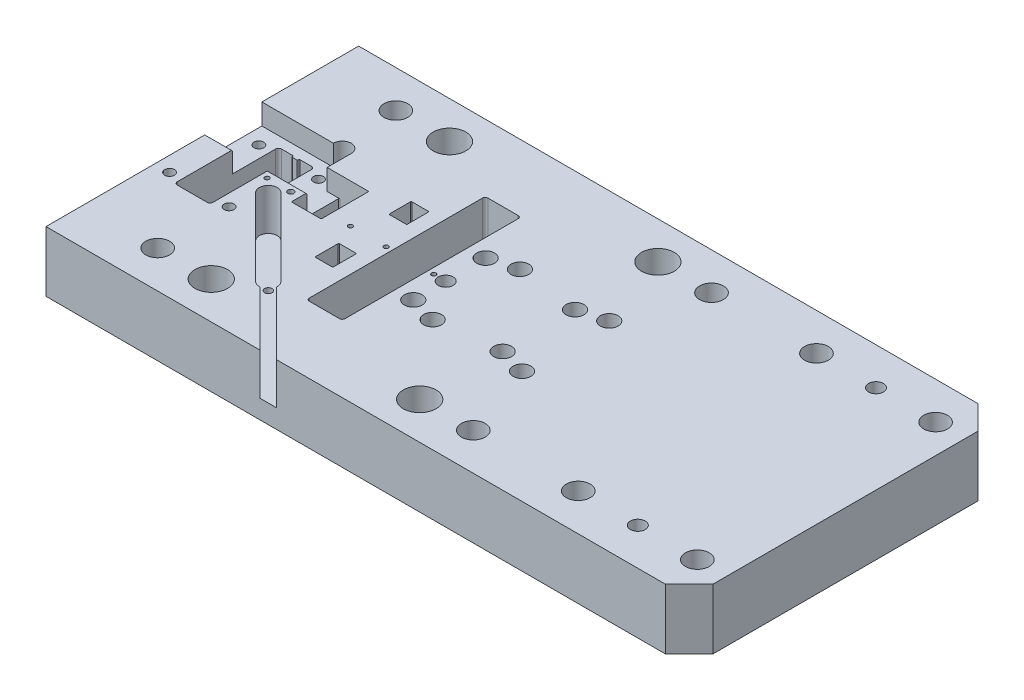
SolidWorks part; units mm, degrees
ref_plane "Front" through (0, 0, 0) normal (0, 0, 1) x (1, 0, 0)
ref_plane "Top" through (0, 0, 0) normal (0, 1, 0) x (1, 0, 0)
ref_plane "Right" through (0, 0, 0) normal (1, 0, 0) x (0, 0, -1)
sketch "Sketch1" plane through (0, 0, 0) normal (0, 0, 1) x (1, 0, 0)
  line L1 (-78, 0) -> (138, 0)
  line L2 (-78, 0) -> (-78, 20.3)
  line L3 (-78, 20.3) -> (138, 20.3)
  line L4 (138, 0) -> (138, 20.3)
  dimension "D1" = 138
  dimension "D2" = 20.3
  dimension "D3" = 78
extrude "Extrude1" add sketch "Sketch1" along normal mid plane 105
ref_plane "Plane1" through (0, 16.3, 0) normal (0, 1, 0) x (-1, 0, 0)
chamfer "Chamfer1" [suppressed] distance 0.5 angle 45
hole_wizard "M6 Tapped Hole1" [suppressed] positions "Sketch9" profile "Sketch8" tap size "M6" standard "ISO"
sketch "Sketch9" plane through (9.0333, 18, 0.7036) normal (0, -1, 0) x (1, 0, 0)
  line L4 (-9.0333, -0.7036) -> (-9.0333, -58.1038) construction
  point P0 (-44.0333, -38.2036)
  dimension "D2" = 37.5
  dimension "D1" = 35
cosmetic thread "Cosmetic Thread1" [suppressed] parameters "D1"=18, "D2"=6
sketch "Sketch8" plane through (-35, 18, -37.5) normal (1, 0, 0) x (0, 0, 1)
  line L0 (0, 0) -> (0, 18)
  line L1 (0, 18) -> (2.5, 18)
  line L2 (2.5, 18) -> (2.5, 0)
  line L5 (2.5, 0) -> (0, 0)
  line L11 (0, -6.35) -> (0, 107.95) construction
  dimension "Thru Tap Drill Dia." = 5
  dimension "Thru Tap Drill Depth" = 18
pattern_linear "LPattern3" [suppressed] count 2 spacing 70 count 2 spacing 75
hole_wizard "Ø6.0 (6.000000) Diameter Hole1" [suppressed] positions "Sketch11" profile "Sketch10" hole size "Ø6.0" standard "ISO"
sketch "Sketch11" plane through (0, 18, 0) normal (0, 1, 0) x (-1, 0, 0)
  line L1 (35, -37.5) -> (50, -37.5) construction
  point P0 (50, -37.5)
  dimension "D1" = 50
sketch "Sketch10" plane through (-50, 18, -37.5) normal (1, 0, 0) x (0, 0, 1)
  line L0 (0, 0) -> (0, 18)
  line L1 (0, 18) -> (3, 18)
  line L2 (3, 18) -> (3, 0)
  line L5 (3, 0) -> (0, 0)
  line L11 (0, -6.35) -> (0, 107.95) construction
  dimension "Thru Hole Dia." = 6
  dimension "Thru Hole Depth" = 18
pattern_linear "LPattern4" [suppressed] count 2 spacing 100 count 2 spacing 75
hole_wizard "CBORE for M6 Hex Socket Head Cap Screw1" positions "Sketch13" profile "Sketch12" counterbore size "M6" standard "ISO" end condition through all
sketch "Sketch13" plane through (0, 20.3, 0) normal (0, 1, 0) x (-1, 0, 0)
  line L0 (0, -52.5) -> (0, 10.8276) construction
  line L2 (-138, -52.5) -> (78, -52.5) construction
  line L3 (78, 52.5) -> (78, -52.5) construction
  point P0 (35, -40)
  dimension "D1" = 40
  dimension "D2" = 70
  dimension "D3" = 78
sketch "Sketch12" plane through (-35, 20.3, -40) normal (1, 0, 0) x (0, 0, 1)
  line L0 (0, 0) -> (0, 20.3)
  line L1 (0, 20.3) -> (3.2, 20.3)
  line L3 (3.2, 20.3) -> (3.2, 11)
  line L4 (3.2, 11) -> (5.5, 11)
  line L5 (5.5, 11) -> (5.5, 0)
  line L7 (5.5, 0) -> (0, 0)
  line L11 (0, -6.35) -> (0, 107.95) construction
  dimension "Thru Hole Dia." = 6.4
  dimension "Thru Hole Depth" = 20.3
  dimension "C'Bore Dia." = 11
  dimension "C'Bore Depth" = 11
pattern_linear "LPattern5" count 2 spacing 70 along (1, 0, 0) count 2 spacing 80 along (0, 0, 1) of "CBORE for M6 Hex Socket Head Cap Screw1"
hole_wizard "Hole1" positions "Sketch15" profile "Sketch14" legacy end condition through all
sketch "Sketch15" plane through (0, 20.3, 0) normal (0, 1, 0) x (-1, 0, 0)
  line L0 (0, -52.5) -> (0, 52.5) construction
  line L3 (0, 0) -> (37.836, 0) construction
  line L4 (78, 52.5) -> (78, -52.5) construction
  point P0 (53, -40)
  dimension "D1" = 40
  dimension "D2" = 106
  dimension "D3" = 78
sketch "Sketch14" plane through (-53, 20.3, -40) normal (1, 0, 0) x (0, 0, 1)
  line L0 (0, 0) -> (0, 20.3)
  line L1 (0, 20.3) -> (4, 20.3)
  line L2 (4, 20.3) -> (4, 0)
  line L3 (4, 0) -> (0, 0)
  line L4 (0, 110) -> (0, -10) construction
  dimension "Diameter" = 8
  dimension "Depth" = 20.3
pattern_linear "LPattern6" count 2 spacing 106 along (1, 0, 0) count 2 spacing 80 along (0, 0, 1) of "Hole1"
hole_wizard "Hole2" positions "Sketch17" profile "Sketch16" legacy end condition through all
sketch "Sketch17" plane through (0, 20.3, 0) normal (0, 1, 0) x (-1, 0, 0)
  line L0 (-35, -12.15) -> (-35, 12.15) construction
  line L1 (-35, 0) -> (0, 0) construction
  line L2 (-14, -14.65) -> (-44, -14.65) construction
  line L3 (-14, 14.65) -> (-44, 14.65) construction
  line L4 (-14, 14.65) -> (-14, -14.65) construction
  line L5 (-44, 14.65) -> (-44, -14.65) construction
  line L6 (-44, 0) -> (0, 0) construction
  line L7 (-5, -12.15) -> (-35, -12.15) construction
  point P0 (-35, 12.15)
  point P1 (-35, -12.15)
  point P9 (-5, -12.15)
  point P11 (-5, 12.15)
  point P12 (-14, -14.65)
  point P14 (-14, 14.65)
  point P16 (-44, 14.65)
  point P18 (-44, -14.65)
  dimension "D1" = 35
  dimension "D2" = 24.3
  dimension "D3" = 30
  dimension "D4" = 2.5
  dimension "D5" = 9
sketch "Sketch16" plane through (35, 20.3, 12.15) normal (1, 0, 0) x (0, 0, 1)
  line L0 (0, 0) -> (0, 20.3)
  line L1 (0, 20.3) -> (3, 20.3)
  line L2 (3, 20.3) -> (3, 0)
  line L3 (3, 0) -> (0, 0)
  line L4 (0, 110) -> (0, -10) construction
  dimension "Diameter" = 6
  dimension "Depth" = 20.3
sketch "Sketch20" plane through (0, 20.3, 0) normal (0, 1, 0) x (1, 0, 0)
  line L4 (-1.933, 30) -> (-12.067, 30)
  line L5 (-1, -29.067) -> (-1, 29.067)
  line L6 (-12.067, -30) -> (-1.933, -30)
  line L7 (-13, 29.067) -> (-13, -29.067)
  line L8 (-1.933, 30) -> (-12.067, 30)
  line L9 (-1, -29.067) -> (-1, 29.067)
  line L10 (-12.067, -30) -> (-1.933, -30)
  line L11 (-13, 29.067) -> (-13, -29.067)
  arc A4 (-1, 29.067) -> (-1.933, 30) centre (-1.933, 29.067) ccw
  arc A5 (-1.933, -30) -> (-1, -29.067) centre (-1.933, -29.067) ccw
  arc A6 (-13, -29.067) -> (-12.067, -30) centre (-12.067, -29.067) ccw
  arc A7 (-12.067, 30) -> (-13, 29.067) centre (-12.067, 29.067) ccw
  arc A8 (-1, 29.067) -> (-1.933, 30) centre (-1.933, 29.067) ccw
  arc A9 (-1.933, -30) -> (-1, -29.067) centre (-1.933, -29.067) ccw
  arc A10 (-13, -29.067) -> (-12.067, -30) centre (-12.067, -29.067) ccw
  arc A11 (-12.067, 30) -> (-13, 29.067) centre (-12.067, 29.067) ccw
  dimension "D1" = 0
extrude "Cut-Extrude2" cut sketch "Sketch20" against normal through all
hole_wizard "Hole3" positions "Sketch22" profile "Sketch21" legacy
sketch "Sketch22" plane through (0, 0, 0) normal (0, -1, 0) x (-1, 0, 0)
  point P0 (-5, -1.2694)
sketch "Sketch21" plane through (5, 0, 1.2694) normal (1, 0, 0) x (0, 0, -1)
  line L0 (0, 0) -> (0, 100)
  line L1 (0, 100) -> (2.5, 100)
  line L2 (2.5, 100) -> (2.5, 5)
  line L3 (2.5, 5) -> (4, 5)
  line L4 (4, 5) -> (4, 0)
  line L5 (4, 0) -> (0, 0)
  line L6 (0, 110) -> (0, -10) construction
  dimension "Diameter" = 5
  dimension "Depth" = 100
  dimension "C-Bore Diameter" = 8
  dimension "C-Bore Depth" = 5
sketch "Sketch23" plane through (0, 20.3, 0) normal (0, 1, 0) x (1, 0, 0)
  line L4 (-18.25, -8.1954) -> (-23.75, -8.1954)
  line L5 (-24, -8.4454) -> (-24, -15.9454)
  line L6 (-23.75, -16.1954) -> (-18.25, -16.1954)
  line L7 (-18, -15.9454) -> (-18, -8.4454)
  line L8 (-18.25, -8.1954) -> (-23.75, -8.1954)
  line L9 (-24, -8.4454) -> (-24, -15.9454)
  line L10 (-23.75, -16.1954) -> (-18.25, -16.1954)
  line L11 (-18, -15.9454) -> (-18, -8.4454)
  line L12 (-18.25, 16.15) -> (-23.75, 16.15)
  line L13 (-24, 15.9) -> (-24, 8.9)
  line L14 (-23.75, 8.65) -> (-18.25, 8.65)
  line L15 (-18, 8.9) -> (-18, 15.9)
  line L16 (-18.25, 16.15) -> (-23.75, 16.15)
  line L17 (-24, 15.9) -> (-24, 8.9)
  line L18 (-23.75, 8.65) -> (-18.25, 8.65)
  line L19 (-18, 8.9) -> (-18, 15.9)
  arc A4 (-23.75, -8.1954) -> (-24, -8.4454) centre (-23.75, -8.4454) ccw
  arc A5 (-24, -15.9454) -> (-23.75, -16.1954) centre (-23.75, -15.9454) ccw
  arc A6 (-18.25, -16.1954) -> (-18, -15.9454) centre (-18.25, -15.9454) ccw
  arc A7 (-18, -8.4454) -> (-18.25, -8.1954) centre (-18.25, -8.4454) ccw
  arc A8 (-23.75, -8.1954) -> (-24, -8.4454) centre (-23.75, -8.4454) ccw
  arc A9 (-24, -15.9454) -> (-23.75, -16.1954) centre (-23.75, -15.9454) ccw
  arc A10 (-18.25, -16.1954) -> (-18, -15.9454) centre (-18.25, -15.9454) ccw
  arc A11 (-18, -8.4454) -> (-18.25, -8.1954) centre (-18.25, -8.4454) ccw
  arc A12 (-23.75, 16.15) -> (-24, 15.9) centre (-23.75, 15.9) ccw
  arc A13 (-24, 8.9) -> (-23.75, 8.65) centre (-23.75, 8.9) ccw
  arc A14 (-18.25, 8.65) -> (-18, 8.9) centre (-18.25, 8.9) ccw
  arc A15 (-18, 15.9) -> (-18.25, 16.15) centre (-18.25, 15.9) ccw
  arc A16 (-23.75, 16.15) -> (-24, 15.9) centre (-23.75, 15.9) ccw
  arc A17 (-24, 8.9) -> (-23.75, 8.65) centre (-23.75, 8.9) ccw
  arc A18 (-18.25, 8.65) -> (-18, 8.9) centre (-18.25, 8.9) ccw
  arc A19 (-18, 15.9) -> (-18.25, 16.15) centre (-18.25, 15.9) ccw
  dimension "D1" = 0
  dimension "D2" = 0
extrude "Cut-Extrude3" cut sketch "Sketch23" against normal through all
sketch "Sketch24" plane through (0, 20.3, 0) normal (0, 1, 0) x (1, 0, 0)
  line L4 (-34.25, 11.9046) -> (-39, 11.9046)
  line L5 (-39, 11.9046) -> (-39, -4.0954)
  line L6 (-39, -4.0954) -> (-34.25, -4.0954)
  line L7 (-34, -3.8454) -> (-34, 11.6546)
  line L8 (-34.25, 11.9046) -> (-39, 11.9046)
  line L9 (-39, 11.9046) -> (-39, -4.0954)
  line L10 (-39, -4.0954) -> (-34.25, -4.0954)
  line L11 (-34, -3.8454) -> (-34, 11.6546)
  arc A2 (-34.25, -4.0954) -> (-34, -3.8454) centre (-34.25, -3.8454) ccw
  arc A3 (-34, 11.6546) -> (-34.25, 11.9046) centre (-34.25, 11.6546) ccw
  arc A4 (-34.25, -4.0954) -> (-34, -3.8454) centre (-34.25, -3.8454) ccw
  arc A5 (-34, 11.6546) -> (-34.25, 11.9046) centre (-34.25, 11.6546) ccw
  dimension "D1" = 0
extrude "Cut-Extrude4" cut sketch "Sketch24" against normal through all
sketch "Sketch25" plane through (0, 20.3, 0) normal (0, 1, 0) x (1, 0, 0)
  line L4 (-43.75, -4.0954) -> (-39, -4.0954)
  line L5 (-44, 11.6546) -> (-44, -3.8454)
  line L6 (-39, 11.9046) -> (-43.75, 11.9046)
  line L7 (-39, -4.0954) -> (-39, 11.9046)
  line L8 (-43.75, -4.0954) -> (-39, -4.0954)
  line L9 (-44, 11.6546) -> (-44, -3.8454)
  line L10 (-39, 11.9046) -> (-43.75, 11.9046)
  line L11 (-39, -4.0954) -> (-39, 11.9046)
  arc A2 (-44, -3.8454) -> (-43.75, -4.0954) centre (-43.75, -3.8454) ccw
  arc A3 (-43.75, 11.9046) -> (-44, 11.6546) centre (-43.75, 11.6546) ccw
  arc A4 (-44, -3.8454) -> (-43.75, -4.0954) centre (-43.75, -3.8454) ccw
  arc A5 (-43.75, 11.9046) -> (-44, 11.6546) centre (-43.75, 11.6546) ccw
  dimension "D1" = 0
extrude "Cut-Extrude5" cut sketch "Sketch25" against normal through all
sketch "Sketch26" plane through (0, 20.3, 0) normal (0, 1, 0) x (1, 0, 0)
  line L0 (-78, -52.5) -> (-78, 52.5) construction
  line L1 (-43.75, 1.1046) -> (-78, 1.1046)
  line L2 (-43.75, 1.1046) -> (-43.75, 11.9046)
  line L3 (-43.75, 11.9046) -> (-78, 11.9046)
  line L4 (-78, 1.1046) -> (-78, 11.9046)
  line L5 (-44, 1.3046) -> (-39, 1.3046) construction
  dimension "D1" = 0.2
extrude "Cut-Extrude6" cut sketch "Sketch26" against normal blind 7
sketch "Sketch27" plane through (0, 20.3, 0) normal (0, 1, 0) x (1, 0, 0)
  line L4 (-64.25, 16.6046) -> (-68, 16.6046)
  line L5 (-57, -17.3954) -> (-57, 15.6046)
  line L6 (-68, -18.3954) -> (-58, -18.3954)
  line L7 (-69, 15.6046) -> (-69, -17.3954)
  line L8 (-64.25, 16.6046) -> (-68, 16.6046)
  line L9 (-57, -17.3954) -> (-57, 15.6046)
  line L10 (-68, -18.3954) -> (-58, -18.3954)
  line L11 (-69, 15.6046) -> (-69, -17.3954)
  line L56 (-64, 16.2546) -> (-64, 16.3546)
  line L57 (-64, 16.2546) -> (-64, 16.3546)
  line L58 (-62.25, 16.0046) -> (-63.75, 16.0046)
  line L59 (-62.25, 16.0046) -> (-63.75, 16.0046)
  line L60 (-62, 16.3546) -> (-62, 16.2546)
  line L61 (-62, 16.3546) -> (-62, 16.2546)
  line L62 (-58, 16.6046) -> (-61.75, 16.6046)
  line L63 (-58, 16.6046) -> (-61.75, 16.6046)
  arc A4 (-57, 15.6046) -> (-58, 16.6046) centre (-58, 15.6046) ccw
  arc A5 (-58, -18.3954) -> (-57, -17.3954) centre (-58, -17.3954) ccw
  arc A6 (-69, -17.3954) -> (-68, -18.3954) centre (-68, -17.3954) ccw
  arc A7 (-68, 16.6046) -> (-69, 15.6046) centre (-68, 15.6046) ccw
  arc A8 (-57, 15.6046) -> (-58, 16.6046) centre (-58, 15.6046) ccw
  arc A9 (-58, -18.3954) -> (-57, -17.3954) centre (-58, -17.3954) ccw
  arc A10 (-69, -17.3954) -> (-68, -18.3954) centre (-68, -17.3954) ccw
  arc A11 (-68, 16.6046) -> (-69, 15.6046) centre (-68, 15.6046) ccw
  arc A56 (-64, 16.3546) -> (-64.25, 16.6046) centre (-64.25, 16.3546) ccw
  arc A57 (-64, 16.3546) -> (-64.25, 16.6046) centre (-64.25, 16.3546) ccw
  arc A58 (-64, 16.2546) -> (-63.75, 16.0046) centre (-63.75, 16.2546) ccw
  arc A59 (-64, 16.2546) -> (-63.75, 16.0046) centre (-63.75, 16.2546) ccw
  arc A60 (-62.25, 16.0046) -> (-62, 16.2546) centre (-62.25, 16.2546) ccw
  arc A61 (-62.25, 16.0046) -> (-62, 16.2546) centre (-62.25, 16.2546) ccw
  arc A62 (-61.75, 16.6046) -> (-62, 16.3546) centre (-61.75, 16.3546) ccw
  arc A63 (-61.75, 16.6046) -> (-62, 16.3546) centre (-61.75, 16.3546) ccw
  dimension "D1" = 0
extrude "Cut-Extrude7" cut sketch "Sketch27" against normal through all
chamfer "Chamfer2" distance 0.3 angle 45 2 edges at (-50.5, 20.3, -1.1046) (-73.5, 20.3, -1.1046)
hole_wizard "Hole4" positions "Sketch29" profile "Sketch28" legacy
sketch "Sketch29" plane through (0, 20.3, 0) normal (0, 1, 0) x (-1, 0, 0)
  point P0 (-1, 1.2694)
  point P3 (15, 1.2694)
  point P6 (27, 1.2694)
  point P12 (55, 1.2694)
sketch "Sketch28" plane through (1, 20.3, 1.2694) normal (1, 0, 0) x (0, 0, 1)
  line L0 (0, 0) -> (0, 3.433)
  line L1 (0, 3.433) -> (0.75, 3)
  line L2 (0.75, 3) -> (0.75, 0)
  line L4 (0.75, 0) -> (0, 0)
  line L6 (0, 3.433) -> (-0.75, 3) construction
  line L7 (0, -4.2442) -> (0, 117.3081) construction
  dimension "Diameter" = 1.5
  dimension "Depth" = 3
  dimension "Drill Angle" = 120
sketch "Sketch30" plane through (0, 20.3, 0) normal (0, 1, 0) x (1, 0, 0)
  line L1 (-78, 11.9046) -> (-48, 11.9046)
  line L2 (-78, 11.9046) -> (-78, 20)
  line L3 (-78, 20) -> (-54, 20)
  line L4 (-48, 11.9046) -> (-48, 20)
  arc A0 (-48, 20) -> (-54, 20) centre (-51, 20) ccw
  dimension "D3" = 6
  dimension "D1" = 20
  dimension "D2" = 30
extrude "Cut-Extrude9" cut sketch "Sketch30" against normal up to surface (7 mm away) up to face at (-49.1604, 13.3, -7.545)
hole_wizard "M4 Tapped Hole1" positions "Sketch32" profile "Sketch31" tap size "M4" standard "ISO"
sketch "Sketch32" plane through (0, 20.3, 0) normal (0, 1, 0) x (1, 0, 0)
  point P0 (-53, -16)
  point P3 (-73, -16)
sketch "Sketch31" plane through (-53, 20.3, 16) normal (1, 0, 0) x (0, 0, 1)
  line L0 (0, 0) -> (0, 15.9914)
  line L1 (0, 15.9914) -> (1.65, 15)
  line L2 (1.65, 15) -> (1.65, 0)
  line L5 (1.65, 0) -> (0, 0)
  line L10 (0, 15.9914) -> (-1.65, 15) construction
  line L11 (0, -6.35) -> (0, 107.95) construction
  dimension "Tap Drill Dia." = 3.3
  dimension "Tap Drill Depth" = 15
  dimension "Drill Angle" = 118
cosmetic thread "Hole Thread1" parameters "D1"=8, "D2"=4
cosmetic thread "Hole Thread2" parameters "D1"=8, "D2"=4
hole_wizard "M4 Tapped Hole2" positions "Sketch34" profile "Sketch33" tap size "M4" standard "ISO"
sketch "Sketch34" plane through (0, 13.3, 0) normal (0, 1, 0) x (1, 0, 0)
  point P0 (-73, 14)
  point P3 (-53, 14)
sketch "Sketch33" plane through (-73, 13.3, -14) normal (1, 0, 0) x (0, 0, 1)
  line L0 (0, 0) -> (0, 15.9914)
  line L1 (0, 15.9914) -> (1.65, 15)
  line L2 (1.65, 15) -> (1.65, 0)
  line L5 (1.65, 0) -> (0, 0)
  line L10 (0, 15.9914) -> (-1.65, 15) construction
  line L11 (0, -6.35) -> (0, 107.95) construction
  dimension "Tap Drill Dia." = 3.3
  dimension "Tap Drill Depth" = 15
  dimension "Drill Angle" = 118
cosmetic thread "Hole Thread3" parameters "D1"=8, "D2"=4
cosmetic thread "Hole Thread4" parameters "D1"=8, "D2"=4
chamfer "Chamfer3" distance 8 angle 45 2 edges at (138, 10.15, -52.5) (138, 10.15, 52.5)
hole_wizard "Hole5" positions "Sketch36" profile "Sketch35" legacy
sketch "Sketch36" plane through (0, 20.3, 0) normal (0, 1, 0) x (1, 0, 0)
  point P0 (88.25, 40)
  point P3 (128.25, 40)
  point P6 (88.25, -40)
  point P9 (128.25, -40)
sketch "Sketch35" plane through (88.25, 20.3, -40) normal (1, 0, 0) x (0, 0, 1)
  line L0 (0, 0) -> (0, 100)
  line L1 (0, 100) -> (4, 100)
  line L2 (4, 100) -> (4, 0)
  line L3 (4, 0) -> (0, 0)
  line L4 (0, 110) -> (0, -10) construction
  dimension "Diameter" = 8
  dimension "Depth" = 100
hole_wizard "M6 Tapped Hole2" positions "Sketch38" profile "Sketch37" tap size "M6" standard "ISO" end condition through all
sketch "Sketch38" plane through (0, 20.3, 0) normal (0, 1, 0) x (1, 0, 0)
  point P3 (108.25, 40)
  point P6 (108.25, -40)
sketch "Sketch37" plane through (108.25, 20.3, -40) normal (1, 0, 0) x (0, 0, 1)
  line L0 (0, 0) -> (0, 20.3)
  line L1 (0, 20.3) -> (2.5, 20.3)
  line L2 (2.5, 20.3) -> (2.5, 0)
  line L5 (2.5, 0) -> (0, 0)
  line L11 (0, -6.35) -> (0, 107.95) construction
  dimension "Thru Tap Drill Dia." = 5
  dimension "Thru Tap Drill Depth" = 20.3
cosmetic thread "Hole Thread5" parameters "D2"=6
cosmetic thread "Hole Thread6" parameters "D2"=6
hole_wizard "Hole6" positions "Sketch40" profile "Sketch39" legacy
sketch "Sketch40" plane through (0, 20.3, 0) normal (0, 1, 0) x (1, 0, 0)
  point P0 (-47, -1.2694)
sketch "Sketch39" plane through (-47, 20.3, 1.2694) normal (1, 0, 0) x (0, 0, 1)
  line L0 (0, 0) -> (0, 5)
  line L1 (0, 5) -> (1, 5)
  line L2 (1, 5) -> (1, 0)
  line L3 (1, 0) -> (0, 0)
  line L4 (0, 110) -> (0, -10) construction
  dimension "Diameter" = 2
  dimension "Depth" = 5
sketch "Sketch41" plane through (0, 20.3, 0) normal (0, 1, 0) x (1, 0, 0)
  line L1 (-48.05, -7.7954) -> (-49.74, -7.7954) construction
  line L2 (-49.74, -3.2709) -> (-49.74, -8.5069) construction
  line L3 (-48.55, -7.7954) -> (-48.55, -9.9794) construction
  line L5 (-48.55, -9.9794) -> (-48.25, -9.9794) construction
  line L6 (-48.25, -9.9794) -> (-48.25, -8.6954) construction
  line L7 (-52.06, -2.7954) -> (-49.94, -2.7954) construction
  line B0 (-52.6533, -7.4489) -> (-26.8439, -33.2583)
  line B1 (-24.5391, -34.1347) -> (-3.1635, -55.5103)
  line B2 (-0.335, -52.6819) -> (-21.7106, -31.3063)
  line B3 (-48.3965, -3.1921) -> (-22.5871, -29.0015)
  line B4 (-3.1635, -55.5103) -> (-0.335, -52.6819)
  arc B5 (-26.8439, -33.2583) -> (-24.5391, -34.1347) centre (-24.7155, -31.1299) ccw
  arc B6 (-22.5871, -29.0015) -> (-21.7106, -31.3063) centre (-24.7155, -31.1299) cw
  arc B7 (-52.6533, -7.4489) -> (-48.3965, -3.1921) centre (-50.5249, -5.3205) cw
  dimension "D1" = 0.3
  dimension "D2" = 5
sketch_block_instance "Block-Utor_senzor_pomika-1"
sketch_block "Block-Utor_senzor_pomika" parameters "D1"=1, "D2"=6.02, "D3"=3.5, "D4"=4, "D5"=33
extrude "Cut-Extrude10" cut sketch "Sketch41" against normal blind 14
hole_wizard "M3 Tapped Hole1" positions "Sketch42" profile "Sketch43" tap size "M3" standard "ISO"
sketch "Sketch42" plane through (0, 6.3, 0) normal (0, 1, 0) x (1, 0, 0)
  point P0 (-36.0292, -19.8162)
sketch "Sketch43" plane through (-36.0292, 6.3, 19.8162) normal (1, 0, 0) x (0, 0, 1)
  line L0 (0, 0) -> (0, 8.2511)
  line L1 (0, 8.2511) -> (1.25, 7.5)
  line L2 (1.25, 7.5) -> (1.25, 0)
  line L5 (1.25, 0) -> (0, 0)
  line L10 (0, 8.2511) -> (-1.25, 7.5) construction
  line L11 (0, -6.35) -> (0, 107.95) construction
  dimension "Tap Drill Dia." = 2.5
  dimension "Tap Drill Depth" = 7.5
  dimension "Drill Angle" = 118
cosmetic thread "Hole Thread7" parameters "D1"=6, "D2"=3
equation "\"D4@LPattern3\" = \"D2@Sketch9\"*2"
equation "\"D3@LPattern4\" = \"D1@Sketch11\"*2"
equation "\"D4@LPattern4\" = \"D2@Sketch9\"*2"
